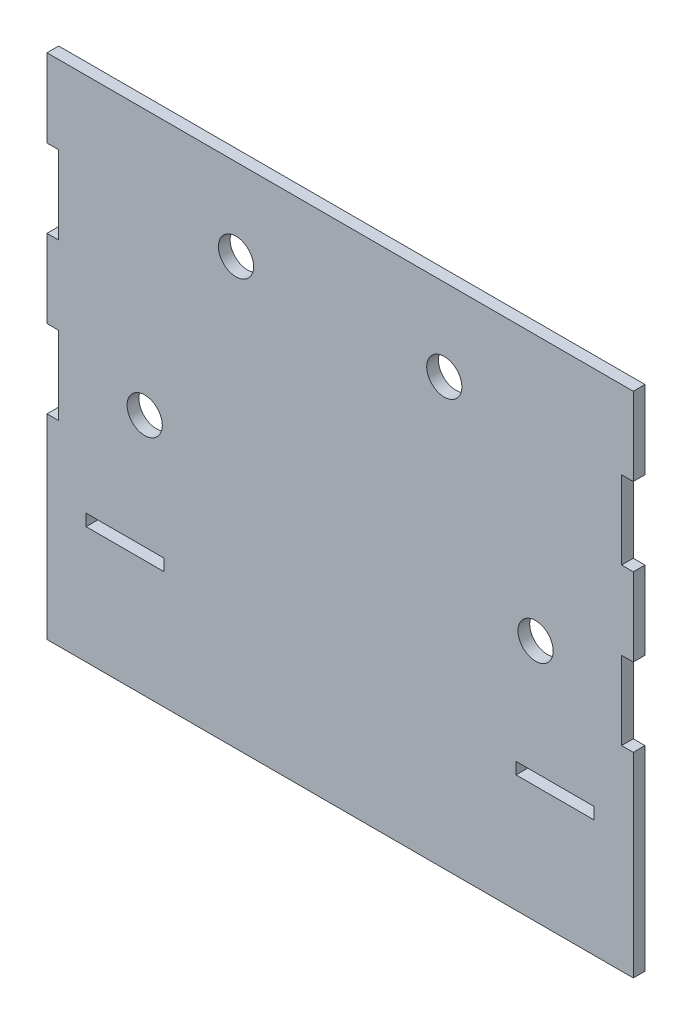
SolidWorks part; units mm, degrees
material "Cedar"
ref_plane "Front Plane" through (0, 0, 0) normal (0, 0, 1) x (1, 0, 0)
ref_plane "Top Plane" through (0, 0, 0) normal (0, 1, 0) x (1, 0, 0)
ref_plane "Right Plane" through (0, 0, 0) normal (1, 0, 0) x (0, 0, -1)
sketch "Sketch1" plane through (0, 0, 0) normal (0, 0, 1) x (1, 0, 0)
  line L1 (-75, -50) -> (75, -50)
  line L2 (-75, -50) -> (-75, 50)
  line L3 (-75, 50) -> (75, 50)
  line L4 (75, -50) -> (75, 50)
  line L5 (-75, -50) -> (75, 50) construction
  line L6 (-75, 50) -> (75, -50) construction
  point P0 (0, 0)
  dimension "D1" = 100
  dimension "D2" = 150
extrude "Boss-Extrude1" add sketch "Sketch1" along normal blind 3
sketch "Sketch2" plane through (0, 0, 3) normal (0, 0, 1) x (1, 0, 0)
  line L0 (75, 30) -> (72, 30)
  line L1 (75, -50) -> (75, 50) construction
  line L2 (72, 30) -> (72, 10)
  line L3 (72, 10) -> (75, 10)
  line L4 (75, -10) -> (72, -10)
  line L5 (72, -10) -> (72, -30)
  line L6 (72, -30) -> (75, -30)
  line L7 (-75, -50) -> (75, -50) construction
  line L8 (75, 50) -> (-75, 50) construction
  line L9 (75, 30) -> (75, 10)
  line L16 (75, -10) -> (75, -30)
  line L35 (0, -25.5074) -> (0, 19.2338) construction
  line L36 (-75, -10) -> (-75, -30)
  line L37 (-75, 30) -> (-75, 10)
  line L38 (-72, -30) -> (-75, -30)
  line L39 (-72, -10) -> (-72, -30)
  line L40 (-75, -10) -> (-72, -10)
  line L41 (-75, 50) -> (-75, -50) construction
  line L46 (-72, 10) -> (-75, 10)
  line L51 (-65, -50) -> (-45, -50)
  line L52 (-65, -50) -> (-65, -47)
  line L53 (-65, -47) -> (-45, -47)
  line L54 (-45, -50) -> (-45, -47)
  line L55 (45, -50) -> (65, -50)
  line L56 (45, -50) -> (45, -47)
  line L57 (45, -47) -> (65, -47)
  line L58 (65, -50) -> (65, -47)
  line L59 (-72, 30) -> (-72, 10)
  line L60 (-75, 30) -> (-72, 30)
  dimension "D1" = 20
  dimension "D2" = 20
  dimension "D3" = 20
  dimension "D4" = 20
  dimension "D5" = 3
  dimension "D6" = 3
  dimension "D8" = 20
  dimension "D9" = 20
  dimension "D10" = 3
  dimension "D11" = 3
  dimension "D12" = 10
  dimension "D13" = 10
extrude "Cut-Extrude1" cut sketch "Sketch2" against normal blind 3
sketch "Sketch3" plane through (0, -50, 0) normal (0, -1, 0) x (1, 0, 0)
  line L1 (-75, 3) -> (75, 3)
  line L2 (-75, 3) -> (-75, 0)
  line L3 (-75, 0) -> (75, 0)
  line L4 (75, 3) -> (75, 0)
extrude "Boss-Extrude2" add sketch "Sketch3" along normal blind 30
sketch "Sketch4" plane through (0, 0, 3) normal (0, 0, 1) x (1, 0, 0)
  line L0 (0, 23.9777) -> (0, -25.2768) construction
sketch "Sketch5" plane through (0, 0, 3) normal (0, 0, 1) x (1, 0, 0)
  circle A0 centre (50, -17.8077) radius 4.5
  circle A1 centre (-50, -17.8077) radius 4.5
extrude "Cut-Extrude2" cut sketch "Sketch5" against normal blind 10
sketch "Sketch6" plane through (0, 0, 0) normal (0, 0, -1) x (-1, 0, 0)
  circle A0 centre (26.6441, 29.0268) radius 4.5
  circle A1 centre (-26.6441, 29.0268) radius 4.5
extrude "Cut-Extrude3" cut sketch "Sketch6" against normal blind 10
